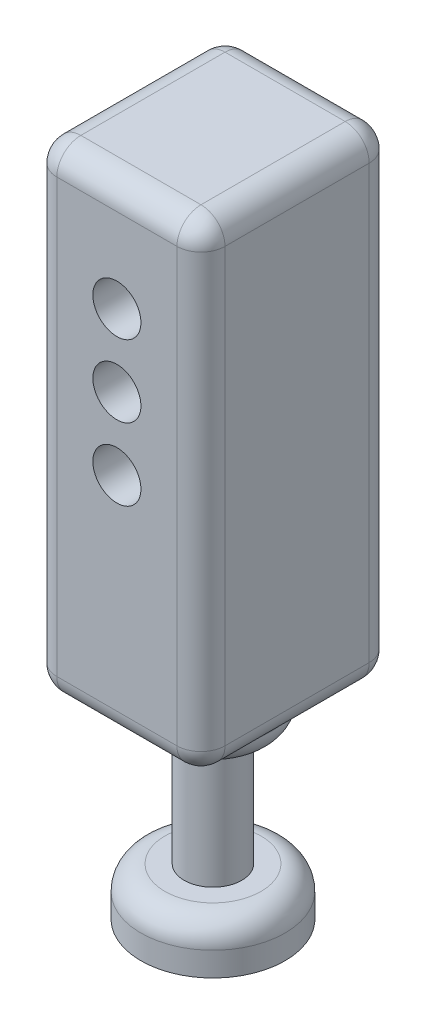
SolidWorks part; units mm, degrees
ref_plane "Front Plane" through (0, 0, 0) normal (0, 0, 1) x (1, 0, 0)
ref_plane "Top Plane" through (0, 0, 0) normal (0, 1, 0) x (1, 0, 0)
ref_plane "Right Plane" through (0, 0, 0) normal (1, 0, 0) x (0, 0, -1)
sketch "Sketch1" plane through (0, 0, 0) normal (0, 0, 1) x (1, 0, 0)
  line L1 (-14.7765, 101.4486) -> (55.2235, 101.4486)
  line L2 (-14.7765, 101.4486) -> (-14.7765, -98.5514)
  line L3 (-14.7765, -98.5514) -> (55.2235, -98.5514)
  line L4 (55.2235, 101.4486) -> (55.2235, -98.5514)
  dimension "D1" = 200
  dimension "D2" = 70
extrude "Boss-Extrude1" add sketch "Sketch1" along normal blind 80
fillet "Fillet1" radius 10 12 edges at (-14.7765, -98.5514, 40) (20.2235, -98.5514, 0) (20.2235, -98.5514, 80) (55.2235, -98.5514, 40) (55.2235, 1.4486, 80) (-14.7765, 1.4486, 80) (55.2235, 1.4486, 0) (-14.7765, 1.4486, 0) (20.2235, 101.4486, 80) (20.2235, 101.4486, 0) (55.2235, 101.4486, 40) (-14.7765, 101.4486, 40)
sketch "Sketch2" plane through (0, -98.5514, 0) normal (0, -1, 0) x (-1, 0, 0)
  circle A0 centre (-20.2235, -40) radius 24.4425
extrude "Boss-Extrude2" add sketch "Sketch2" along normal blind 15
fillet "Fillet3" radius 10 1 edges at (44.666, -113.5514, 40)
sketch "Sketch3" plane through (0, -113.5514, 0) normal (0, -1, 0) x (1, 0, 0)
  circle A0 centre (20.1947, 39.9845) radius 12
extrude "Boss-Extrude3" add sketch "Sketch3" along normal blind 50
sketch "Sketch4" plane through (0, -163.5514, 0) normal (0, -1, 0) x (-1, 0, 0)
  circle A0 centre (-20.1947, -39.9845) radius 30
extrude "Boss-Extrude4" add sketch "Sketch4" along normal blind 20
fillet "Fillet4" radius 10 1 edges at (50.1947, -163.5514, 39.9845)
sketch "Sketch5" plane through (0, 0, 80) normal (0, 0, 1) x (1, 0, 0)
  circle A0 centre (20.2235, 56.4486) radius 10
  circle A1 centre (20.2235, 26.4486) radius 10
  circle A2 centre (20.2235, -3.5514) radius 10
  dimension "D1" = 20
extrude "Cut-Extrude1" cut sketch "Sketch5" against normal blind 80
